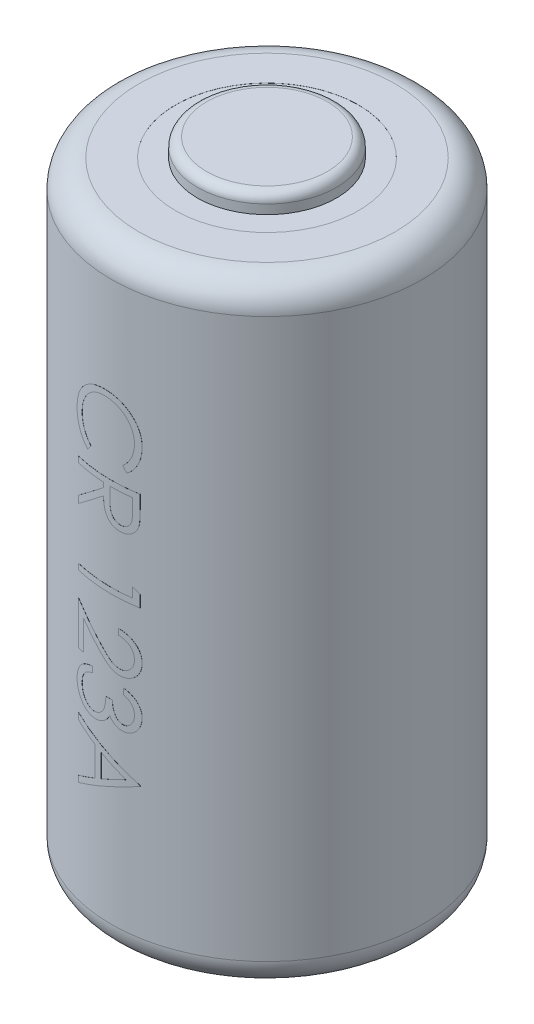
SolidWorks part; units mm, degrees
ref_plane "Ebene vorne" through (0, 0, 0) normal (0, 0, 1) x (1, 0, 0)
ref_plane "Ebene oben" through (0, 0, 0) normal (0, 1, 0) x (1, 0, 0)
ref_plane "Ebene rechts" through (0, 0, 0) normal (1, 0, 0) x (0, 0, -1)
sketch "Skizze1" plane through (0, 0, 0) normal (0, 1, 0) x (1, 0, 0)
  circle A0 centre (0, 0) radius 8.5
  dimension "D1" = 17
extrude "Aufsatz-Linear austragen1" add sketch "Skizze1" along normal blind 33.5
sketch "Skizze2" plane through (0, 33.5, 0) normal (0, 1, 0) x (1, 0, 0)
  circle A0 centre (0, 0) radius 3.8
extrude "Aufsatz-Linear austragen2" add sketch "Skizze2" along normal blind 1
fillet "Verrundung1" radius 1.5 2 edges at (0, 0, 8.5) (0, 33.5, 8.5)
fillet "Verrundung2" radius 0.5 1 edges at (0, 34.5, 3.8)
sketch "Skizze3" plane through (0, 33.5, 0) normal (0, 1, 0) x (1, 0, 0)
  circle A0 centre (0, 0) radius 5
  circle A1 centre (0, 0) radius 3.8
  dimension "D1" = 10
  dimension "D2" = 7.6
extrude "Schnitt-Linear austragen1" cut sketch "Skizze3" against normal blind 0.005
sketch "Skizze4" plane through (0, 0, 0) normal (0, 0, 1) x (1, 0, 0)
  line L0 (-2.0456, 26.9015) -> (-2.0456, 5.1704) construction
  text T0 "CR 123A"
extrude "Aufsatz-Linear austragen3" add sketch "Skizze4" along normal offset from surface (8.5005 mm away) 0.005
